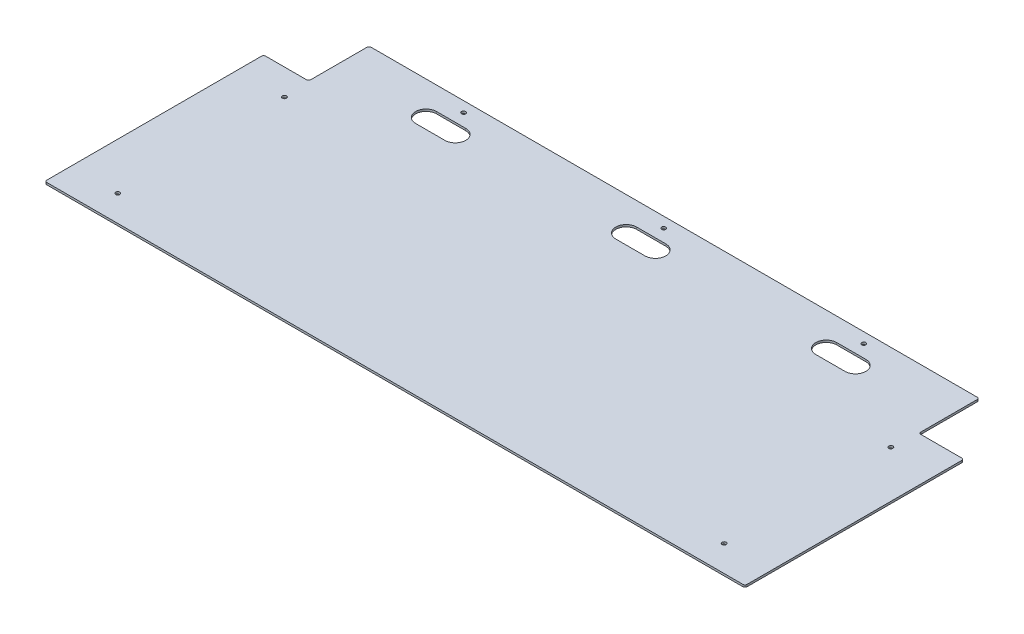
SolidWorks part; units mm, degrees
material "PC High Viscosity"
ref_plane "Front Plane" through (0, 0, 0) normal (0, 0, 1) x (1, 0, 0)
ref_plane "Top Plane" through (0, 0, 0) normal (0, 1, 0) x (1, 0, 0)
ref_plane "Right Plane" through (0, 0, 0) normal (1, 0, 0) x (0, 0, -1)
sketch "Sketch1" plane through (0, 0, 0) normal (0, 1, 0) x (1, 0, 0)
  line L1 (0, 0) -> (1066.8, 0)
  line L2 (0, 0) -> (0, 333.375)
  line L3 (0, 333.375) -> (1066.8, 333.375)
  line L4 (1066.8, 0) -> (1066.8, 333.375)
  dimension "D1" = 333.375
  dimension "D2" = 1066.8
extrude "Boss-Extrude1" add sketch "Sketch1" along normal blind 3.175
sketch "Sketch2" plane through (0, 3.175, 0) normal (0, 1, 0) x (1, 0, 0)
  line L0 (1066.8, 333.375) -> (0, 333.375) construction
  line L1 (68.58, 333.375) -> (998.22, 333.375)
  line L2 (68.58, 333.375) -> (68.58, 425.45)
  line L3 (68.58, 425.45) -> (998.22, 425.45)
  line L4 (998.22, 333.375) -> (998.22, 425.45)
  line L5 (0, 0) -> (1066.8, 0) construction
  line L6 (0, 333.375) -> (0, 0) construction
  point P6 (533.4, 0)
  point P7 (533.4, 333.375)
  dimension "D1" = 68.58
  dimension "D2" = 92.075
extrude "Boss-Extrude2" add sketch "Sketch2" against normal up to surface (3.175 mm away) up to face at (533.4, 0, -166.6875)
hole_wizard "1/4 (0.25) Diameter Hole1" positions "Sketch4" profile "Sketch5" hole size "1/4" standard "ANSI Inch" end condition through all
sketch "Sketch4" plane through (0, 0, 0) normal (0, -1, 0) x (-1, 0, 0)
  line L0 (-533.4, 0) -> (-533.4, 425.45) construction
  line L1 (0, 0) -> (-1066.8, 0) construction
  line L2 (-998.22, 425.45) -> (-68.58, 425.45) construction
  line L3 (-1066.8, 166.6875) -> (0, 166.6875) construction
  line L4 (-1066.8, 0) -> (-1066.8, 333.375) construction
  line L5 (0, 333.375) -> (0, 0) construction
  point P30 (-228.6, 409.575)
  point P31 (-533.4, 409.575)
  point P32 (-838.2, 409.575)
  point P33 (-995.3625, 293.6875)
  point P44 (-995.3625, 39.6875)
  point P46 (-71.4375, 293.6875)
  point P47 (-71.4375, 39.6875)
  dimension "D1" = 304.8
  dimension "D2" = 71.4375
  dimension "D3" = 15.875
  dimension "D4" = 127
sketch "Sketch5" plane through (71.4375, 0, -39.6875) normal (1, 0, 0) x (0, 0, -1)
  line L0 (0, 0) -> (0, 3.175)
  line L1 (0, 3.175) -> (3.175, 3.175)
  line L2 (3.175, 3.175) -> (3.175, 0)
  line L5 (3.175, 0) -> (0, 0)
  line L11 (0, -6.35) -> (0, 107.95) construction
  dimension "Thru Hole Dia." = 6.35
  dimension "Thru Hole Depth" = 3.175
hole_wizard "1/4 (0.25) Diameter Hole2" positions "Sketch6" profile "Sketch7" hole size "1/4" standard "ANSI Inch"
sketch "Sketch6" plane through (0, 0, 0) normal (0, -1, 0) x (-1, 0, 0)
  line L0 (-1066.8, 166.6875) -> (0, 166.6875) construction
  line L1 (-1066.8, 0) -> (-1066.8, 333.375) construction
  line L2 (0, 333.375) -> (0, 0) construction
  line L4 (-533.4, 425.45) -> (-533.4, 0) construction
  line L5 (-998.22, 425.45) -> (-68.58, 425.45) construction
  line L6 (0, 0) -> (-1066.8, 0) construction
  point P0 (-995.3625, 39.6875)
  point P2 (-995.3625, 293.6875)
  point P21 (-71.4375, 39.6875)
  point P22 (-71.4375, 293.6875)
  dimension "D1" = 127
  dimension "D2" = 71.4375
sketch "Sketch7" plane through (995.3625, 0, -39.6875) normal (1, 0, 0) x (0, 0, -1)
  line L0 (0, 0) -> (0, 3.175)
  line L1 (0, 3.175) -> (3.175, 3.175)
  line L2 (3.175, 3.175) -> (3.175, 0)
  line L5 (3.175, 0) -> (0, 0)
  line L11 (0, -6.35) -> (0, 107.95) construction
  dimension "Thru Hole Dia." = 6.35
  dimension "Thru Hole Depth" = 3.175
fillet "Fillet1" radius 3.175 8 edges at (0, 1.5875, -333.375) (68.58, 1.5875, -333.375) (68.58, 1.5875, -425.45) (0, 1.5875, 0) (1066.8, 1.5875, 0) (998.22, 1.5875, -425.45) (1066.8, 1.5875, -333.375) (998.22, 1.5875, -333.375)
sketch "Sketch9" plane through (0, 0, 0) normal (0, -1, 0) x (1, 0, 0)
  line L0 (860.425, -374.65) -> (815.975, -374.65) construction
  line L3 (860.425, -390.525) -> (815.975, -390.525)
  line L4 (860.425, -358.775) -> (815.975, -358.775)
  line L5 (555.625, -374.65) -> (511.175, -374.65) construction
  line L6 (555.625, -390.525) -> (511.175, -390.525)
  line L7 (555.625, -358.775) -> (511.175, -358.775)
  line L8 (250.825, -374.65) -> (206.375, -374.65) construction
  line L9 (250.825, -390.525) -> (206.375, -390.525)
  line L10 (250.825, -358.775) -> (206.375, -358.775)
  arc A2 (860.425, -390.525) -> (860.425, -358.775) centre (860.425, -374.65) ccw
  arc A3 (815.975, -358.775) -> (815.975, -390.525) centre (815.975, -374.65) ccw
  circle A4 centre (838.2, -409.575) radius 3.175 construction
  arc A5 (555.625, -390.525) -> (555.625, -358.775) centre (555.625, -374.65) ccw
  arc A6 (511.175, -358.775) -> (511.175, -390.525) centre (511.175, -374.65) ccw
  arc A7 (250.825, -390.525) -> (250.825, -358.775) centre (250.825, -374.65) ccw
  arc A8 (206.375, -358.775) -> (206.375, -390.525) centre (206.375, -374.65) ccw
  point P2 (838.2, -374.65)
  point P10 (533.4, -409.575)
  point P11 (838.2, -409.575)
  point P15 (533.4, -374.65)
  point P22 (228.6, -374.65)
  dimension "D1" = 31.75
  dimension "D2" = 76.2
  dimension "D3" = 19.05
  dimension "D4" = 3
extrude "Cut-Extrude1" cut sketch "Sketch9" against normal through all
